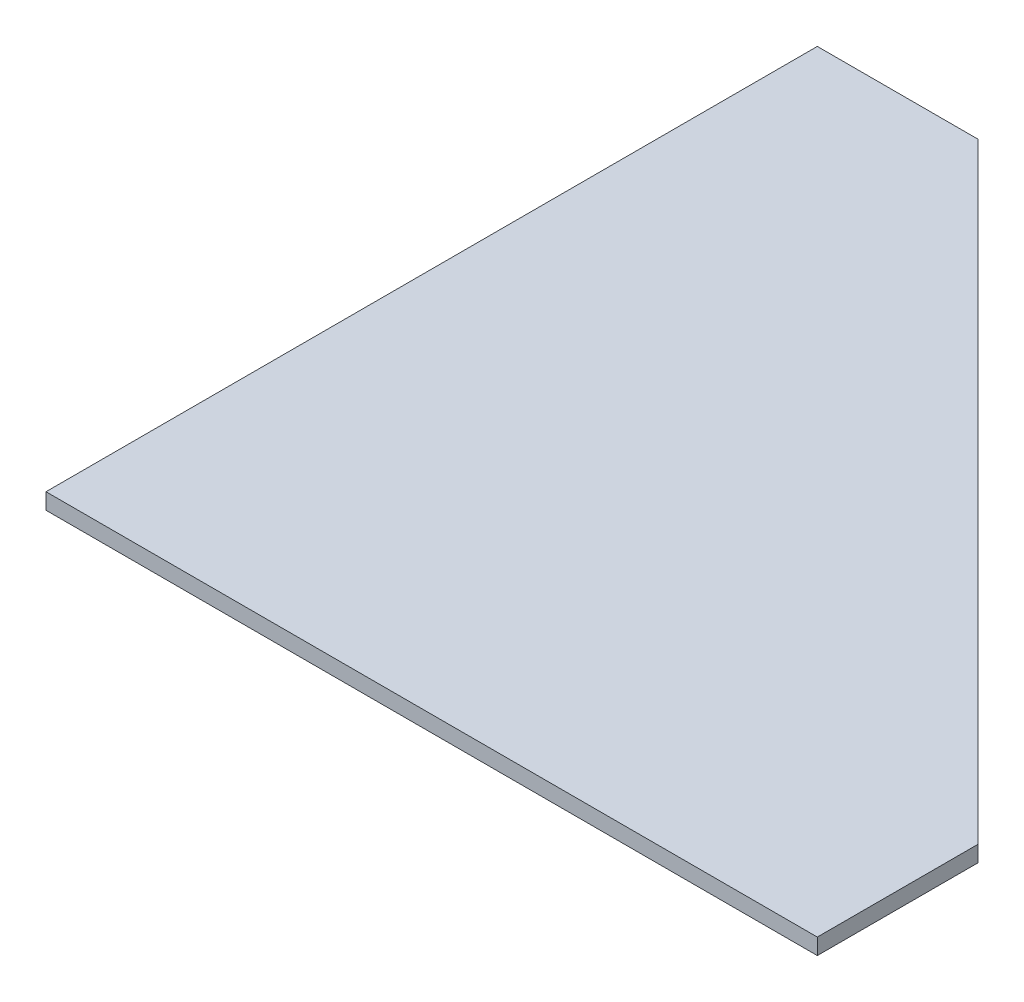
SolidWorks part; units mm, degrees
ref_plane "Front Plane" through (0, 0, 0) normal (0, 0, 1) x (1, 0, 0)
ref_plane "Top Plane" through (0, 0, 0) normal (0, 1, 0) x (1, 0, 0)
ref_plane "Right Plane" through (0, 0, 0) normal (1, 0, 0) x (0, 0, -1)
sketch "Sketch1" plane through (0, 0, 0) normal (0, 1, 0) x (1, 0, 0)
  line L0 (0, 0) -> (609.6, 0)
  line L1 (609.6, 0) -> (609.6, 127)
  line L2 (609.6, 127) -> (127, 609.6)
  line L3 (127, 609.6) -> (0, 609.6)
  line L4 (0, 609.6) -> (0, 0)
  dimension "D1" = 45
  dimension "D2" = 609.6
  dimension "D3" = 609.6
  dimension "D4" = 127
extrude "Boss-Extrude1" add sketch "Sketch1" along normal blind 12.7
